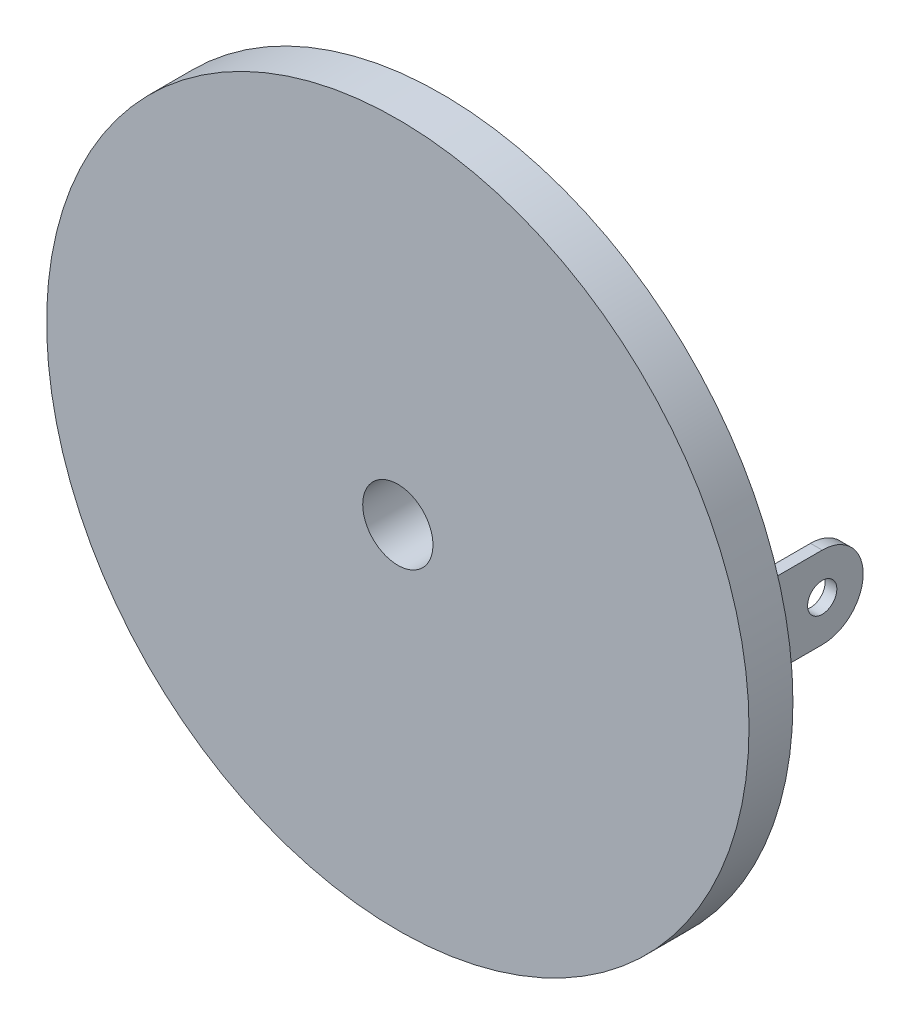
SolidWorks part; units mm, degrees
ref_plane "Plan de face" through (0, 0, 0) normal (0, 0, 1) x (1, 0, 0)
ref_plane "Plan de dessus" through (0, 0, 0) normal (0, 1, 0) x (1, 0, 0)
ref_plane "Plan de droite" through (0, 0, 0) normal (1, 0, 0) x (0, 0, -1)
sketch "Esquisse1" plane through (0, 0, 0) normal (0, 0, 1) x (1, 0, 0)
  circle A0 centre (0, 0) radius 12
extrude "Extrusion1" add sketch "Esquisse1" along normal blind 1.5
sketch "Esquisse2" plane through (0, 0, 0) normal (0, 0, -1) x (-1, 0, 0)
  line L0 (-12.8188, 0) -> (5.0276, 0) construction
  line L1 (0, 5.1893) -> (0, -1.9552) construction
  line L2 (-12.4954, 1.4) -> (-4.9394, 1.4) construction
  line L3 (-12.4954, -1.4) -> (-4.9394, -1.4) construction
  line L4 (-9, 6.2183) -> (-9, -4.6601) construction
  line L5 (-9.4, 4.4542) -> (-9.4, -4.6601) construction
  line L6 (-12, 4.1896) -> (-12, -5.9243) construction
  line L7 (9.4, 1.4) -> (9, 1.4)
  line L8 (-9.4, 1.4) -> (-9, 1.4)
  line L9 (-9.4, 1.4) -> (-9.4, -1.4)
  line L10 (-9.4, -1.4) -> (-9, -1.4)
  line L11 (-9, 1.4) -> (-9, -1.4)
  line L12 (9.4, 1.4) -> (9.4, -1.4)
  line L13 (9.4, -1.4) -> (9, -1.4)
  line L14 (9, 1.4) -> (9, -1.4)
  dimension "D1" = 1.4
  dimension "D2" = 1.4
  dimension "D3" = 3
  dimension "D4" = 0.4
extrude "Extrusion2" add sketch "Esquisse2" along normal blind 5
sketch "Esquisse3" plane through (0, 0, 0) normal (0, 0, -1) x (-1, 0, 0)
  circle A0 centre (0, 0) radius 4.2
extrude "Extrusion3" add sketch "Esquisse3" along normal blind 2
sketch "Esquisse4" plane through (9.4, 0, 0) normal (1, 0, 0) x (0, 0, -1)
  line L0 (5.9293, 0) -> (-3.1469, 0) construction
  line L1 (5, 1.909) -> (5, -2.2912) construction
  line L2 (3.6, -2.2912) -> (3.6, 1.909) construction
  line L3 (3.6, 1.4) -> (3.6, 1.5114)
  line L4 (3.6, 1.5114) -> (5.1222, 1.5114)
  line L5 (5.1222, 1.5114) -> (5.1222, -1.492)
  line L6 (5.1222, -1.492) -> (3.6, -1.492)
  line L7 (3.6, -1.492) -> (3.6, -1.4)
  circle A0 centre (3.6, 0) radius 0.5
  arc A1 (3.6, -1.4) -> (3.6, 1.4) centre (3.6, 0) ccw
  dimension "D1" = 1.4
extrude "Enlèv. mat.-Extru.1" cut sketch "Esquisse4" against normal through all
sketch "Esquisse5" plane through (0, 0, -2) normal (0, 0, -1) x (-1, 0, 0)
  circle A0 centre (0, 0) radius 1.2
extrude "Enlèv. mat.-Extru.2" cut sketch "Esquisse5" against normal through all
